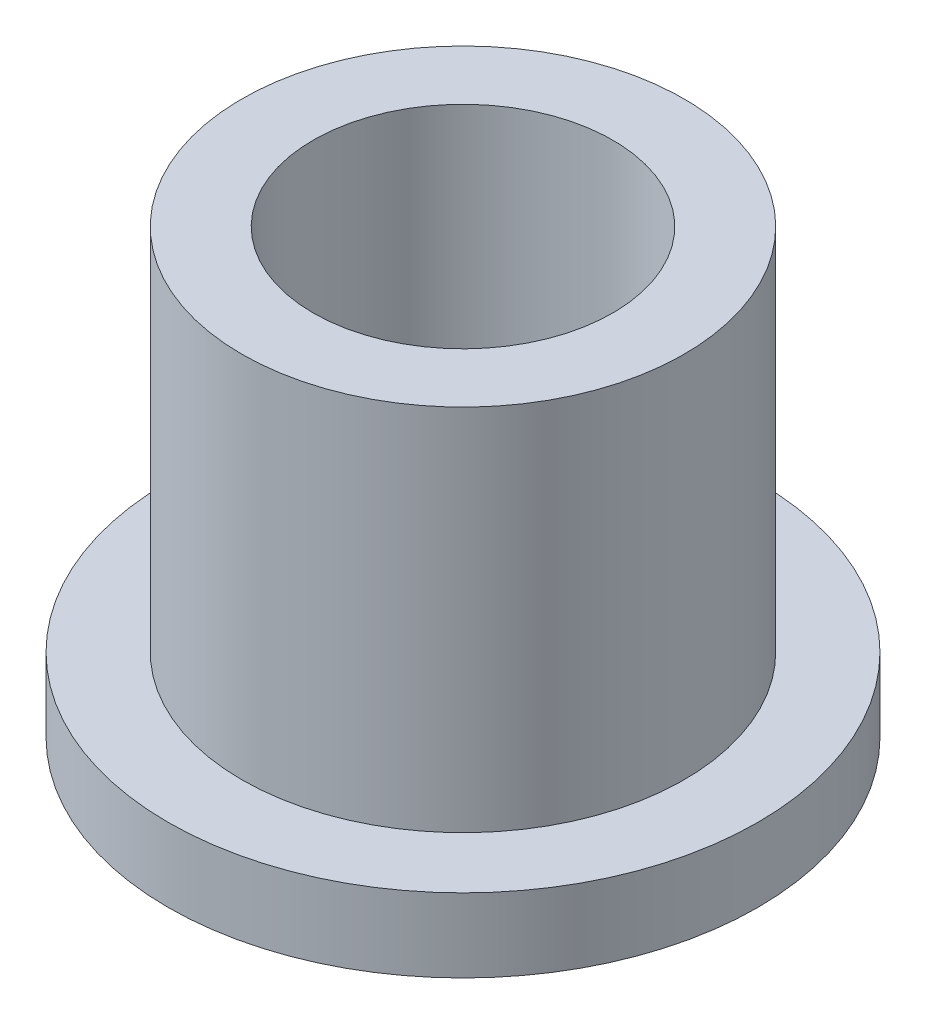
SolidWorks part; units mm, degrees
material "Delrin 2700 NC010, Low Viscosity Acetal Copolymer (SS)"
ref_plane "Front" through (0, 0, 0) normal (0, 0, 1) x (1, 0, 0)
ref_plane "Top" through (0, 0, 0) normal (0, 1, 0) x (1, 0, 0)
ref_plane "Right" through (0, 0, 0) normal (1, 0, 0) x (0, 0, -1)
sketch "Sketch1" plane through (0, 0, 0) normal (0, 1, 0) x (1, 0, 0)
  circle A0 centre (0, 0) radius 3.2258
  circle A1 centre (0, 0) radius 4.7625
  circle A2 centre (0, 0) radius 6.35
  dimension "ID" = 6.4516
  dimension "OD" = 9.525
  dimension "FlangeOD" = 12.7
sketch "Sketch2" plane through (0, 0, 0) normal (0, 1, 0) x (1, 0, 0)
  circle A0 centre (0, 0) radius 3.2258 construction
  circle A1 centre (0, 0) radius 4.7625 construction
  circle A2 centre (0, 0) radius 3.2258
  circle A3 centre (0, 0) radius 4.7625
extrude "Boss-Extrude1" add sketch "Sketch2" along normal blind 9.525
sketch "Sketch3" plane through (0, 0, 0) normal (0, 1, 0) x (1, 0, 0)
  circle A0 centre (0, 0) radius 6.35 construction
  circle A1 centre (0, 0) radius 4.7625 construction
  circle A2 centre (0, 0) radius 6.35
  circle A3 centre (0, 0) radius 4.7625
extrude "Boss-Extrude2" add sketch "Sketch3" along normal blind 1.5875
